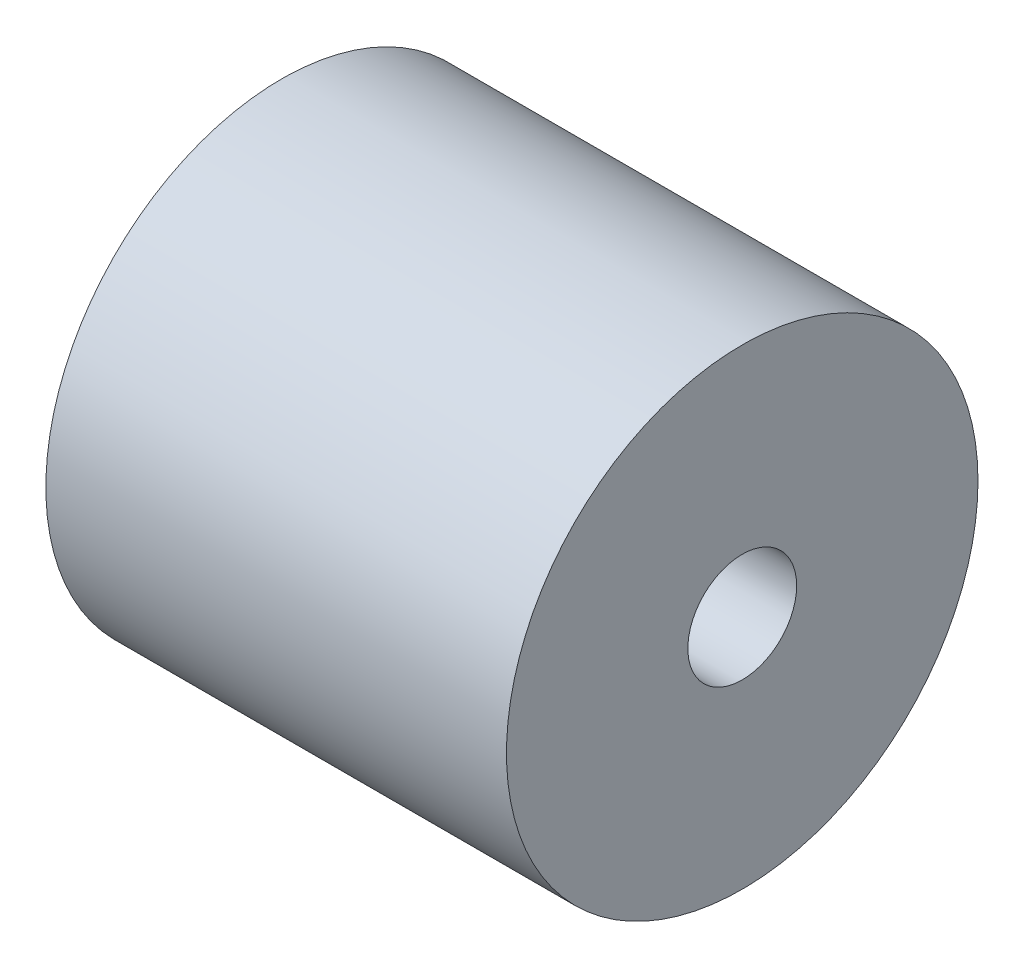
SolidWorks part; units mm, degrees
material "7075-T6, Plate (SS)"
ref_plane "Front Plane" through (0, 0, 0) normal (0, 0, 1) x (1, 0, 0)
ref_plane "Top Plane" through (0, 0, 0) normal (0, 1, 0) x (1, 0, 0)
ref_plane "Right Plane" through (0, 0, 0) normal (1, 0, 0) x (0, 0, -1)
sketch "Sketch1" plane through (0, 0, 0) normal (1, 0, 0) x (0, 0, -1)
  circle A0 centre (0, 0) radius 6.5
  circle A1 centre (0, 0) radius 1.5
  dimension "D1" = 3
  dimension "D2" = 13
extrude "Boss-Extrude1" add sketch "Sketch1" along normal blind 12.7
ref_plane "Plane1" [suppressed] through (0, -6.5, 0) normal (0, -1, 0) x (-1, 0, 0)
hole_wizard "M3x0.5 Tapped Hole1" [suppressed] positions "Sketch3" profile "Sketch4" tap size "M3x0.5" standard "ANSI Metric"
sketch "Sketch3" [suppressed] plane through (0, -6.5, 0) normal (0, -1, 0) x (-1, 0, 0)
  point P0 (-10.1049, 0)
sketch "Sketch4" plane through (10.1049, -6.5, 0) normal (1, 0, 0) x (0, 0, -1)
  line L0 (0, 0) -> (0, 5)
  line L1 (0, 5) -> (1.25, 5)
  line L2 (1.25, 5) -> (1.25, 0)
  line L5 (1.25, 0) -> (0, 0)
  line L11 (0, -6.35) -> (0, 107.95) construction
  dimension "Thru Tap Drill Dia." = 2.5
  dimension "Thru Tap Drill Depth" = 5
cosmetic thread "Hole Thread1" [suppressed] parameters "D2"=3
